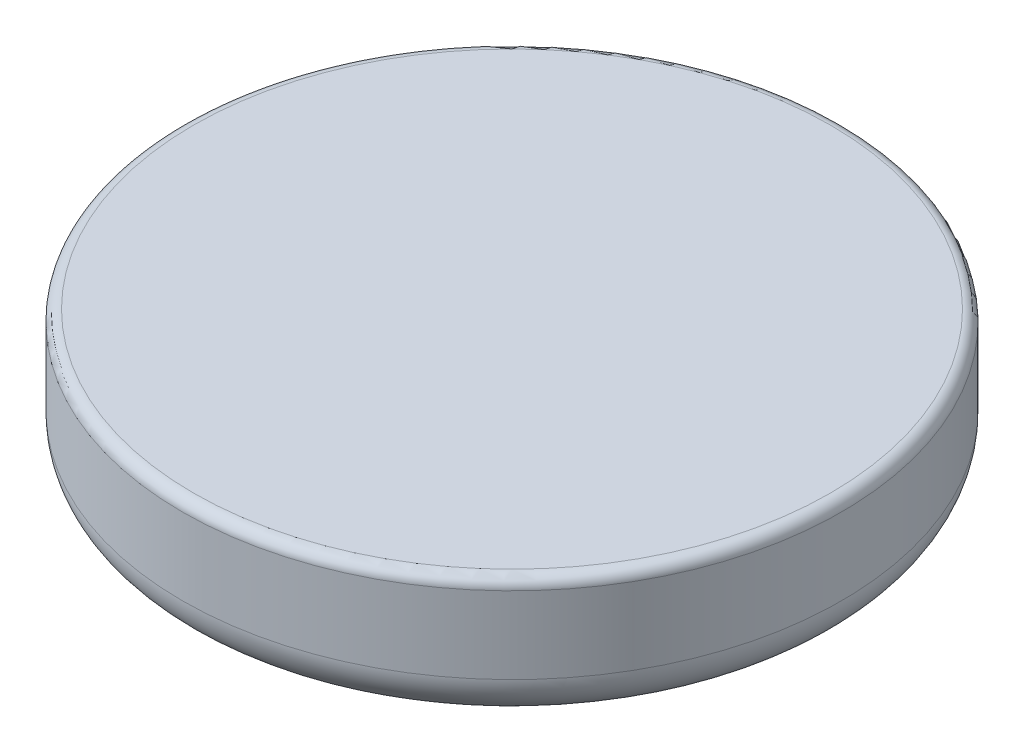
SolidWorks part; units mm, degrees
ref_plane "Front Plane" through (0, 0, 0) normal (0, 0, 1) x (1, 0, 0)
ref_plane "Top Plane" through (0, 0, 0) normal (0, 1, 0) x (1, 0, 0)
ref_plane "Right Plane" through (0, 0, 0) normal (1, 0, 0) x (0, 0, -1)
other "Configuration Table"
sketch "Sketch1" plane through (0, 0, 0) normal (0, 1, 0) x (1, 0, 0)
  circle A0 centre (0, 0) radius 7.5
  dimension "D1" = 15
extrude "Boss-Extrude1" add sketch "Sketch1" along normal blind 3
fillet "Fillet1" radius 1 1 edges at (0, 0, 7.5)
sketch "Sketch2" plane through (0, 0, 0) normal (0, -1, 0) x (1, 0, 0)
  line L0 (-0.7, -0.7) -> (-0.7, -2.55)
  line L1 (0.7, 2.55) -> (-0.7, 2.55)
  line L2 (0.7, 2.55) -> (0.7, 0.7)
  line L3 (0.7, -2.55) -> (-0.7, -2.55)
  line L4 (-0.7, 2.55) -> (-0.7, 0.7)
  line L5 (0.7, 2.55) -> (-0.7, -2.55) construction
  line L6 (0.7, -2.55) -> (-0.7, 2.55) construction
  line L7 (2.55, 0.7) -> (0.7, 0.7)
  line L8 (2.55, 0.7) -> (2.55, -0.7)
  line L9 (2.55, -0.7) -> (0.7, -0.7)
  line L10 (-2.55, 0.7) -> (-2.55, -0.7)
  line L11 (2.55, 0.7) -> (-2.55, -0.7) construction
  line L12 (2.55, -0.7) -> (-2.55, 0.7) construction
  line L13 (-0.7, 0.7) -> (-2.55, 0.7)
  line L14 (0.7, -0.7) -> (0.7, -2.55)
  line L15 (-0.7, -0.7) -> (-2.55, -0.7)
  point P0 (0, 0)
  point P6 (0, 0)
  dimension "D1" = 5.1
  dimension "D2" = 1.4
extrude "Cut-Extrude1" cut sketch "Sketch2" against normal blind 2
fillet "Fillet2" radius 0.25 9 edges at (0, 3, 7.5) (-0.7, 0, 1.625) (0.7, 0, 1.625) (-1.625, 0, -0.7) (-1.625, 0, 0.7) (1.625, 0, 0.7) (1.625, 0, -0.7) (0.7, 0, -1.625) (-0.7, 0, -1.625)
